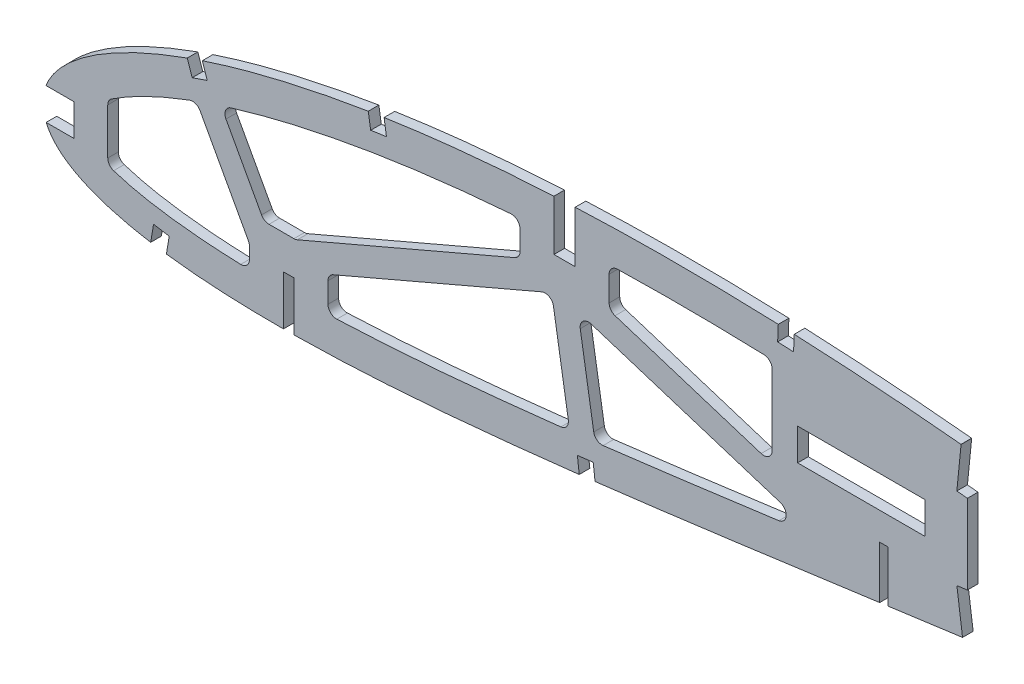
SolidWorks part; units mm, degrees
material "Plywood"
ref_plane "Front Plane" through (0, 0, 0) normal (0, 0, 1) x (1, 0, 0)
ref_plane "Top Plane" through (0, 0, 0) normal (0, 1, 0) x (1, 0, 0)
ref_plane "Right Plane" through (0, 0, 0) normal (1, 0, 0) x (0, 0, -1)
curve "Curve1"
  spline degree 3 poles (452.1031, 0.7048, 0) (452.0685, 0.7262, 0) (451.9301, 0.8117, 0) (451.6183, 1.003, 0) (451.099, 1.3216, 0) (450.372, 1.7653, 0) (449.438, 2.3329, 0) (448.2963, 3.0204, 0) (446.9478, 3.8257, 0) (445.3928, 4.7448, 0) (443.6314, 5.7736, 0) (441.6643, 6.9077, 0) (439.4916, 8.1409, 0) (437.1143, 9.468, 0) (434.5331, 10.8828, 0) (431.7485, 12.3789, 0) (428.7615, 13.9486, 0) (425.5733, 15.5853, 0) (422.1844, 17.2798, 0) (418.5964, 19.0251, 0) (414.8106, 20.8125, 0) (410.8282, 22.6325, 0) (406.6515, 24.4776, 0) (402.2816, 26.3365, 0) (397.7212, 28.201, 0) (392.972, 30.0605, 0) (388.0369, 31.9065, 0) (382.9178, 33.7272, 0) (377.6186, 35.5144, 0) (372.1418, 37.2567, 0) (366.4913, 38.9446, 0) (360.6704, 40.5671, 0) (354.684, 42.1159, 0) (348.5359, 43.5797, 0) (342.2312, 44.9487, 0) (335.775, 46.2147, 0) (329.1727, 47.3651, 0) (322.4425, 48.3989, 0) (315.6929, 49.2588, 0) (308.9571, 50.1023, 0) (302.2314, 50.8946, 0) (295.4235, 51.6533, 0) (288.5399, 52.3742, 0) (281.5875, 53.055, 0) (274.5733, 53.6928, 0) (267.5046, 54.2857, 0) (260.3883, 54.8303, 0) (253.2318, 55.3259, 0) (246.0422, 55.768, 0) (238.8272, 56.1563, 0) (231.5941, 56.4881, 0) (224.3504, 56.7611, 0) (217.1039, 56.9737, 0) (209.862, 57.1238, 0) (202.6326, 57.2105, 0) (195.4232, 57.2315, 0) (188.2416, 57.1863, 0) (181.0954, 57.0734, 0) (173.9924, 56.8912, 0) (166.9401, 56.6395, 0) (159.9462, 56.3182, 0) (153.0184, 55.9248, 0) (146.164, 55.4618, 0) (139.3909, 54.9271, 0) (132.7063, 54.3206, 0) (126.1174, 53.645, 0) (119.6314, 52.8983, 0) (113.2554, 52.0826, 0) (106.9962, 51.1996, 0) (100.8609, 50.2488, 0) (94.8561, 49.2329, 0) (88.9882, 48.153, 0) (83.2635, 47.0122, 0) (77.6882, 45.8109, 0) (72.2682, 44.5525, 0) (67.0092, 43.2395, 0) (61.9167, 41.874, 0) (56.9959, 40.4594, 0) (52.2519, 38.999, 0) (47.6902, 37.4943, 0) (43.3141, 35.951, 0) (39.1291, 34.3702, 0) (35.1384, 32.7568, 0) (31.3466, 31.113, 0) (27.7567, 29.4439, 0) (24.3726, 27.7512, 0) (21.1967, 26.0397, 0) (18.2324, 24.3122, 0) (15.4823, 22.5717, 0) (12.9477, 20.8227, 0) (10.632, 19.0664, 0) (8.5361, 17.307, 0) (6.6613, 15.5474, 0) (5.0102, 13.7886, 0) (3.5829, 12.0339, 0) (2.3811, 10.2847, 0) (1.4051, 8.5424, 0) (0.6571, 6.8085, 0) (0.1363, 5.084, 0) (-0.1488, 3.3712, 0) (-0.2197, 1.669, 0) (-0.0731, 0.5555, 0) (0, 0, 0) knots 0 0 0 0 0.000254 0.001015 0.002283 0.004057 0.006331 0.009105 0.012374 0.016134 0.02038 0.025106 0.030306 0.035972 0.0421 0.048678 0.055702 0.06316 0.071046 0.07935 0.088063 0.097176 0.106678 0.116562 0.126814 0.137428 0.148394 0.1597 0.171338 0.183298 0.19557 0.208144 0.221012 0.234162 0.247587 0.261277 0.275223 0.289414 0.303771 0.317689 0.331784 0.34604 0.360444 0.374983 0.38964 0.404403 0.419257 0.434187 0.449177 0.464215 0.479284 0.49437 0.509458 0.524532 0.539579 0.554583 0.56953 0.584403 0.599191 0.613877 0.628447 0.642889 0.657186 0.671326 0.685294 0.699078 0.712665 0.726043 0.739198 0.752118 0.764792 0.777208 0.789356 0.801224 0.812804 0.824083 0.835055 0.84571 0.856038 0.866034 0.875689 0.884998 0.893953 0.902553 0.910789 0.918661 0.926166 0.933303 0.940071 0.946475 0.952518 0.958205 0.963547 0.968557 0.97325 0.977651 0.981787 0.985694 0.989415 0.993001 0.996508 1 1 1 1
curve "Curve2"
  spline degree 3 poles (0, 0, 0) (0.1161, -0.5481, 0) (0.3488, -1.6467, 0) (0.9811, -3.2283, 0) (1.8173, -4.7487, 0) (2.8749, -6.2038, 0) (4.147, -7.5932, 0) (5.6306, -8.9184, 0) (7.3243, -10.1787, 0) (9.226, -11.3735, 0) (11.3328, -12.5041, 0) (13.6425, -13.5697, 0) (16.1528, -14.5701, 0) (18.8611, -15.5039, 0) (21.764, -16.3724, 0) (24.8588, -17.1737, 0) (28.1419, -17.9088, 0) (31.6103, -18.5759, 0) (35.26, -19.1755, 0) (39.0874, -19.7075, 0) (43.0885, -20.172, 0) (47.2594, -20.5682, 0) (51.596, -20.8969, 0) (56.0938, -21.1583, 0) (60.7487, -21.3533, 0) (65.556, -21.481, 0) (70.5112, -21.5436, 0) (75.6096, -21.5419, 0) (80.8464, -21.4754, 0) (86.2171, -21.3479, 0) (91.7164, -21.1586, 0) (97.3395, -20.9096, 0) (103.0813, -20.6036, 0) (108.9365, -20.2416, 0) (114.9002, -19.8251, 0) (120.967, -19.3576, 0) (127.1315, -18.8401, 0) (133.3883, -18.2757, 0) (139.7319, -17.6673, 0) (146.1567, -17.0167, 0) (152.6572, -16.327, 0) (159.2275, -15.6004, 0) (165.862, -14.8409, 0) (172.5546, -14.0497, 0) (179.2998, -13.2315, 0) (186.0911, -12.3877, 0) (192.923, -11.5217, 0) (199.7891, -10.6375, 0) (206.6832, -9.7349, 0) (213.5994, -8.8205, 0) (220.5311, -7.8935, 0) (227.4721, -6.9586, 0) (234.4161, -6.0188, 0) (241.3564, -5.0743, 0) (248.2868, -4.1291, 0) (255.2009, -3.1857, 0) (262.0918, -2.2442, 0) (268.9535, -1.3094, 0) (275.779, -0.3811, 0) (282.5619, 0.5389, 0) (289.2958, 1.4477, 0) (295.9744, 2.3443, 0) (302.5907, 3.228, 0) (309.138, 4.0992, 0) (315.5119, 4.9314, 0) (321.6955, 5.769, 0) (327.7099, 6.4556, 0) (333.6493, 7.0417, 0) (339.52, 7.5222, 0) (345.315, 7.9041, 0) (351.0275, 8.19, 0) (356.6509, 8.3839, 0) (362.1779, 8.4917, 0) (367.6017, 8.516, 0) (372.9148, 8.4647, 0) (378.1105, 8.3417, 0) (383.1813, 8.1528, 0) (388.1203, 7.9042, 0) (392.9205, 7.6027, 0) (397.5745, 7.2527, 0) (402.076, 6.8625, 0) (406.4179, 6.4377, 0) (410.5937, 5.9833, 0) (414.5972, 5.5086, 0) (418.4221, 5.0169, 0) (422.0625, 4.5163, 0) (425.5126, 4.0117, 0) (428.7669, 3.5097, 0) (431.8204, 3.015, 0) (434.6681, 2.5342, 0) (437.3055, 2.0718, 0) (439.7281, 1.6323, 0) (441.9324, 1.2212, 0) (443.9143, 0.8406, 0) (445.6709, 0.4968, 0) (447.199, 0.1913, 0) (448.4964, -0.0716, 0) (449.5609, -0.2909, 0) (450.3908, -0.463, 0) (450.9844, -0.5881, 0) (451.3411, -0.6626, 0) (451.4997, -0.6964, 0) (451.5393, -0.7048, 0) knots 0 0 0 0 0.003638 0.007293 0.011028 0.014901 0.018963 0.023258 0.027821 0.032679 0.037853 0.043362 0.049215 0.055422 0.061989 0.068918 0.076211 0.083868 0.091887 0.100266 0.109 0.118085 0.127515 0.137285 0.147388 0.157816 0.168563 0.179619 0.190977 0.202627 0.21456 0.226767 0.239236 0.251959 0.264924 0.27812 0.291536 0.30516 0.318981 0.332985 0.347163 0.361499 0.375981 0.390597 0.405333 0.420175 0.43511 0.450124 0.465203 0.480333 0.495501 0.51069 0.525887 0.541078 0.556247 0.571382 0.586466 0.601485 0.616424 0.631269 0.646007 0.660621 0.675098 0.689423 0.703582 0.716908 0.730009 0.742952 0.755726 0.76832 0.780724 0.792927 0.804916 0.816679 0.828204 0.839475 0.850481 0.861208 0.871639 0.881763 0.891564 0.901027 0.910139 0.918884 0.927249 0.935221 0.942785 0.949928 0.956638 0.962904 0.968712 0.974054 0.978918 0.983297 0.98718 0.990561 0.993433 0.995791 0.99763 0.998946 0.999737 1 1 1 1
sketch "Sketch1" plane through (0, 0, 0) normal (0, 0, 1) x (1, 0, 0)
  line L24 (435.3301, 0.6787) -> (439.1729, -1.6142)
  line L25 (434.7872, -0.6787) -> (439.1729, -1.6142)
  spline S4 degree 3 poles (0, 0) (0.1118, -0.5277) (0.3359, -1.5856) (0.9447, -3.1085) (1.7499, -4.5725) (2.7683, -5.9736) (3.9931, -7.3115) (5.4217, -8.5876) (7.0526, -9.8011) (8.8837, -10.9516) (10.9124, -12.0402) (13.1363, -13.0663) (15.5535, -14.0296) (18.1613, -14.9287) (20.9565, -15.765) (23.9365, -16.5366) (27.0978, -17.2444) (30.4375, -17.8867) (33.9519, -18.4641) (37.6373, -18.9763) (41.49, -19.4236) (45.5061, -19.8051) (49.6818, -20.1216) (54.0128, -20.3734) (58.4949, -20.5611) (63.1239, -20.6841) (67.8952, -20.7443) (72.8045, -20.7427) (77.847, -20.6787) (83.0184, -20.5559) (88.3137, -20.3736) (93.7282, -20.1339) (99.2569, -19.8392) (104.895, -19.4906) (110.6374, -19.0896) (116.4791, -18.6394) (122.4149, -18.1411) (128.4396, -17.5977) (134.5478, -17.0118) (140.7343, -16.3853) (146.9936, -15.7212) (153.3201, -15.0216) (159.7085, -14.2903) (166.1528, -13.5285) (172.6478, -12.7406) (179.1872, -11.9281) (185.7655, -11.0942) (192.377, -10.2428) (199.0153, -9.3738) (205.6749, -8.4933) (212.3494, -7.6007) (219.0329, -6.7005) (225.7193, -5.7955) (232.4021, -4.886) (239.0753, -3.9759) (245.7329, -3.0675) (252.3682, -2.161) (258.9753, -1.2608) (265.5476, -0.3669) (272.0789, 0.5189) (278.563, 1.394) (284.9937, 2.2573) (291.3645, 3.1082) (297.669, 3.9471) (303.8064, 4.7484) (309.7606, 5.555) (315.5518, 6.2161) (321.2709, 6.7805) (326.9238, 7.2431) (332.5038, 7.6108) (338.0044, 7.8861) (343.4191, 8.0729) (348.7411, 8.1767) (353.9637, 8.2001) (359.0797, 8.1506) (364.0826, 8.0323) (368.9653, 7.8503) (373.7211, 7.6109) (378.3431, 7.3206) (382.8245, 6.9836) (387.159, 6.6079) (391.3398, 6.1989) (395.3607, 5.7613) (399.2157, 5.3043) (402.8986, 4.8308) (406.404, 4.3487) (409.7261, 3.8629) (412.8597, 3.3795) (415.7999, 2.9031) (418.5419, 2.4402) (421.0815, 1.9949) (423.4142, 1.5717) (425.5368, 1.1759) (427.445, 0.8095) (429.1365, 0.4784) (430.6079, 0.1842) (431.8572, -0.0689) (432.8822, -0.2801) (433.6813, -0.4458) (434.2529, -0.5663) (434.5964, -0.638) (434.749, -0.6706) (434.7872, -0.6787) knots 0 0 0 0 0.003638 0.007293 0.011028 0.014901 0.018963 0.023258 0.027821 0.032679 0.037853 0.043362 0.049215 0.055422 0.061989 0.068918 0.076211 0.083868 0.091887 0.100266 0.109 0.118085 0.127515 0.137285 0.147388 0.157816 0.168563 0.179619 0.190977 0.202627 0.21456 0.226767 0.239236 0.251959 0.264924 0.27812 0.291536 0.30516 0.318981 0.332985 0.347163 0.361499 0.375981 0.390597 0.405333 0.420175 0.43511 0.450124 0.465203 0.480333 0.495501 0.51069 0.525887 0.541078 0.556247 0.571382 0.586466 0.601485 0.616424 0.631269 0.646007 0.660621 0.675098 0.689423 0.703582 0.716908 0.730009 0.742952 0.755726 0.76832 0.780724 0.792927 0.804916 0.816679 0.828204 0.839475 0.850481 0.861208 0.871639 0.881763 0.891564 0.901027 0.910139 0.918884 0.927249 0.935221 0.942785 0.949928 0.956638 0.962904 0.968712 0.974054 0.978918 0.983297 0.98718 0.990561 0.993433 0.995791 0.99763 0.998946 0.999737 1 1 1 1
  spline S5 degree 3 poles (435.3301, 0.6787) (435.2968, 0.6993) (435.1635, 0.7816) (434.8632, 0.9658) (434.3632, 1.2726) (433.6632, 1.6998) (432.7638, 2.2463) (431.6645, 2.9084) (430.3661, 3.6837) (428.8687, 4.5688) (427.1727, 5.5594) (425.2785, 6.6514) (423.1865, 7.8389) (420.8974, 9.1168) (418.4119, 10.4791) (415.7306, 11.9197) (412.8545, 13.4311) (409.7845, 15.0071) (406.5213, 16.6387) (403.0665, 18.3192) (399.4211, 20.0403) (395.5865, 21.7928) (391.5647, 23.5695) (387.357, 25.3594) (382.9657, 27.1547) (378.3927, 28.9452) (373.6407, 30.7228) (368.7116, 32.4759) (363.609, 34.1968) (358.3353, 35.8745) (352.8945, 37.4998) (347.2896, 39.0621) (341.5252, 40.5534) (335.6052, 41.9629) (329.5344, 43.2811) (323.3177, 44.5002) (316.9603, 45.6079) (310.4799, 46.6033) (303.9807, 47.4313) (297.4948, 48.2435) (291.0186, 49.0064) (284.4633, 49.737) (277.8351, 50.4311) (271.1406, 51.0867) (264.3866, 51.7008) (257.5802, 52.2717) (250.7279, 52.7961) (243.8369, 53.2733) (236.914, 53.699) (229.9667, 54.0729) (223.0019, 54.3924) (216.027, 54.6553) (209.0493, 54.86) (202.0761, 55.0045) (195.1149, 55.088) (188.173, 55.1082) (181.2578, 55.0647) (174.3767, 54.956) (167.5373, 54.7806) (160.7467, 54.5381) (154.0122, 54.2288) (147.3414, 53.85) (140.7414, 53.4041) (134.2195, 52.8893) (127.7829, 52.3053) (121.4385, 51.6548) (115.1931, 50.9357) (109.0536, 50.1503) (103.0266, 49.3001) (97.119, 48.3846) (91.3369, 47.4064) (85.6868, 46.3665) (80.1745, 45.2681) (74.806, 44.1113) (69.5871, 42.8996) (64.5231, 41.6353) (59.6196, 40.3205) (54.8814, 38.9584) (50.3134, 37.5521) (45.9209, 36.1032) (41.7071, 34.6172) (37.6774, 33.0951) (33.8348, 31.5415) (30.1837, 29.9587) (26.7269, 28.3515) (23.4684, 26.7216) (20.4104, 25.0737) (17.5559, 23.4102) (14.9079, 21.7343) (12.4673, 20.0502) (10.2376, 18.359) (8.2194, 16.6649) (6.4142, 14.9706) (4.8244, 13.2771) (3.45, 11.5875) (2.2928, 9.9031) (1.353, 8.2255) (0.6327, 6.5559) (0.1312, 4.8953) (-0.1433, 3.2462) (-0.2116, 1.607) (-0.0704, 0.5349) (0, 0) knots 0 0 0 0 0.000254 0.001015 0.002283 0.004057 0.006331 0.009105 0.012374 0.016134 0.02038 0.025106 0.030306 0.035972 0.0421 0.048678 0.055702 0.06316 0.071046 0.07935 0.088063 0.097176 0.106678 0.116562 0.126814 0.137428 0.148394 0.1597 0.171338 0.183298 0.19557 0.208144 0.221012 0.234162 0.247587 0.261277 0.275223 0.289414 0.303771 0.317689 0.331784 0.34604 0.360444 0.374983 0.38964 0.404403 0.419257 0.434187 0.449177 0.464215 0.479284 0.49437 0.509458 0.524532 0.539579 0.554583 0.56953 0.584403 0.599191 0.613877 0.628447 0.642889 0.657186 0.671326 0.685294 0.699078 0.712665 0.726043 0.739198 0.752118 0.764792 0.777208 0.789356 0.801224 0.812804 0.824083 0.835055 0.84571 0.856038 0.866034 0.875689 0.884998 0.893953 0.902553 0.910789 0.918661 0.926166 0.933303 0.940071 0.946475 0.952518 0.958205 0.963547 0.968557 0.97325 0.977651 0.981787 0.985694 0.989415 0.993001 0.996508 1 1 1 1
extrude "Boss-Extrude1" add sketch "Sketch1" along normal blind 3.175
sketch "Sketch2" plane through (0, 0, 0) normal (0, 0, -1) x (-1, 0, 0)
  line L0 (-252.7944, 13.2215) -> (-250.2544, 13.2215)
  line L1 (-250.2544, -2.1152) -> (-250.2544, -3.9863)
  line L2 (-252.7944, 13.2215) -> (-252.7944, -2.1152)
  line L4 (-250.2544, -3.9863) -> (-252.7944, -3.0508)
  line L5 (-252.7944, -3.0508) -> (-252.7944, -2.1152)
  line L7 (-159.1319, 54.4222) -> (-159.1319, 39.0391)
  line L8 (-159.1319, 39.0391) -> (-152.7819, 39.0391)
  line L9 (-152.7819, 54.4222) -> (-152.7819, 57.6454)
  line L10 (-74.9944, -5.9288) -> (-74.9944, -20.1418)
  line L12 (-152.7819, 57.6454) -> (-159.1319, 55.5409)
  line L13 (-159.1319, 55.5409) -> (-159.1319, 54.4222)
  line L14 (-71.8194, -5.9288) -> (-71.8194, -20.1418)
  line L16 (-74.9944, -5.9288) -> (-71.8194, -5.9288)
  line L17 (-71.8194, -20.1418) -> (-71.8194, -22.1459)
  line L19 (-152.7819, 54.4222) -> (-152.7819, 39.0391)
  line L20 (-71.8194, -22.1459) -> (-74.9944, -20.9764)
  line L21 (-74.9944, -20.9764) -> (-74.9944, -20.1418)
  line L22 (-250.2544, 13.2215) -> (-250.2544, -2.1152)
extrude "Cut-Extrude1" cut sketch "Sketch2" against normal blind 7.62
sketch "Sketch3" plane through (0, 0, 0) normal (0, 0, -1) x (-1, 0, 0)
  circle A1 centre (-292.3838, 26.2554) radius 6.35
extrude "Cut-Extrude2" cut sketch "Sketch3" against normal blind 7.62
sketch "Sketch4" plane through (0, 0, 3.175) normal (0, 0, 1) x (1, 0, 0)
  line L0 (274.6066, 50.6647) -> (273.3497, 38.0281)
  line L1 (274.6066, 50.6647) -> (273.3497, 38.0281)
  line L2 (276.5088, 37.7139) -> (277.7874, 50.3428)
  line L3 (276.5088, 37.7139) -> (277.7874, 50.3428)
  line L4 (278.2022, 1.3477) -> (276.5088, 13.9346)
  line L5 (278.2022, 1.3477) -> (276.5088, 13.9346)
  line L6 (273.3622, 13.5108) -> (275.0576, 0.9245)
  line L7 (273.3622, 13.5108) -> (275.0576, 0.9245)
  line L8 (224.4836, 49.6431) -> (224.6991, 54.396)
  line L9 (224.4836, 49.6431) -> (224.6991, 54.396)
  line L10 (165.0827, -13.6872) -> (164.5226, -8.9534)
  line L11 (165.0827, -13.6872) -> (164.5226, -8.9534)
  line L12 (102.6454, 44.5104) -> (101.9324, 49.2278)
  line L13 (102.6454, 44.5104) -> (101.9324, 49.2278)
  line L14 (36.8388, -18.5812) -> (37.6418, -13.8082)
  line L15 (36.8388, -18.5812) -> (37.6418, -13.8082)
  line L16 (49.0205, 32.2539) -> (47.492, 36.7462)
  line L17 (49.0205, 32.2539) -> (47.492, 36.7462)
  line L18 (9.0835, -2.7147) -> (9.0835, 6.8103)
  line L19 (9.0835, -2.7147) -> (9.0835, 6.8103)
  line L20 (-0.4415, 6.8103) -> (9.0835, 6.8103)
  line L21 (-0.4415, 6.8103) -> (9.0835, 6.8103)
  line L22 (32.9524, -13.0236) -> (32.1659, -17.7312)
  line L23 (32.9524, -13.0236) -> (32.1659, -17.7312)
  line L24 (97.1897, 48.4826) -> (97.9364, 43.7986)
  line L25 (97.1897, 48.4826) -> (97.9364, 43.7986)
  line L26 (159.7931, -9.5131) -> (160.3442, -14.2455)
  line L27 (159.7931, -9.5131) -> (160.3442, -14.2455)
  line L28 (42.9896, 35.1929) -> (44.512, 30.7197)
  line L29 (42.9896, 35.1929) -> (44.512, 30.7197)
  line L30 (-0.4415, -2.7147) -> (9.0835, -2.7147)
  line L31 (-0.4415, -2.7147) -> (9.0835, -2.7147)
  line L32 (219.9134, 54.5992) -> (219.7258, 49.8498)
  line L33 (219.9134, 54.5992) -> (219.7258, 49.8498)
  line L34 (276.5088, 13.9346) -> (276.5088, 37.7139)
  line L35 (273.3497, 38.0281) -> (276.5088, 37.7139)
  line L36 (276.5088, 13.9346) -> (273.3622, 13.5108)
  line L37 (275.0576, 0.9245) -> (278.2022, 1.3477)
  line L38 (219.7258, 49.8498) -> (224.4836, 49.6431)
  line L39 (224.6991, 54.396) -> (219.9134, 54.5992)
  line L40 (159.7931, -9.5131) -> (164.5226, -8.9534)
  line L41 (165.0827, -13.6872) -> (160.3442, -14.2455)
  line L42 (42.9896, 35.1929) -> (47.492, 36.7462)
  line L43 (44.512, 30.7197) -> (49.0205, 32.2539)
  line L44 (97.1897, 48.4826) -> (101.9324, 49.2278)
  line L45 (102.6454, 44.5104) -> (97.9364, 43.7986)
  line L46 (-0.4415, 6.8103) -> (-0.4415, -2.7147)
  line L47 (32.9524, -13.0236) -> (37.6418, -13.8082)
  line L48 (36.8388, -18.5812) -> (32.1659, -17.7312)
  line L49 (277.7874, 50.3428) -> (274.6066, 50.6647)
  line L50 (275.0576, 0.9245) -> (275.0576, -18.8331)
  line L51 (225.7088, 31.0179) -> (263.8088, 31.0179)
  line L52 (225.7088, 31.0179) -> (225.7088, 21.4929)
  line L53 (225.7088, 21.4929) -> (263.8088, 21.4929)
  line L54 (263.8088, 31.0179) -> (263.8088, 21.4929)
  line L55 (446.0862, 59.9441) -> (446.0862, -18.8331)
  line L56 (446.0862, -18.8331) -> (275.0576, -18.8331)
  line L57 (274.6066, 50.6647) -> (274.6066, 59.9441)
  line L58 (274.6066, 59.9441) -> (446.0862, 59.9441)
  line L59 (32.1659, -17.7312) -> (31.5691, -21.3035)
  line L60 (31.5691, -21.3035) -> (36.2028, -22.0776)
  line L61 (36.2028, -22.0776) -> (36.8388, -18.5812)
  circle A0 centre (292.3838, 26.2554) radius 6.35 construction
  circle A1 centre (292.3838, 26.2554) radius 6.35
  point P40 (263.8088, 26.2554)
  dimension "D1" = 9.525
  dimension "D2" = 38.1
  dimension "D3" = 12.7
extrude "Cut-Extrude3" cut sketch "Sketch4" against normal through all
sketch "Sketch5" plane through (0, 0, 3.175) normal (0, 0, 1) x (1, 0, 0)
  line L0 (0.7643, 6.8103) -> (9.0835, 6.8103) construction
  line L1 (0.7643, 6.8103) -> (9.0835, 6.8103) construction
  line L2 (0.803, -2.7147) -> (9.0835, -2.7147) construction
  line L3 (0.803, -2.7147) -> (9.0835, -2.7147) construction
  line L4 (273.3622, 13.5108) -> (275.0576, 0.9245) construction
  line L5 (273.3622, 13.5108) -> (275.0576, 0.9245) construction
  line L6 (274.6066, 50.6647) -> (273.3497, 38.0281) construction
  line L7 (274.6066, 50.6647) -> (273.3497, 38.0281) construction
  line L8 (19.2435, 12.3749) -> (19.2435, -4.5391)
  line L9 (9.0835, -2.7147) -> (9.0835, 6.8103) construction
  line L10 (61.6594, 4.2312) -> (46.7663, 31.4868) construction
  line L11 (44.512, 30.7197) -> (49.0205, 32.2539) construction
  line L12 (85.1544, 4.2312) -> (142.6219, 28.8791) construction
  line L13 (169.2919, 28.8791) -> (240.0944, 6.4173) construction
  line L14 (155.9569, 28.8791) -> (162.1578, -9.2332) construction
  line L15 (159.7931, -9.5131) -> (164.5226, -8.9534) construction
  line L16 (66.0011, 4.2312) -> (50.1097, 33.3137)
  line L17 (85.1544, 0.0856) -> (152.2877, 28.8791)
  line L18 (152.1093, 28.8026) -> (158.3973, -9.8451)
  line L19 (159.9871, 27.8339) -> (238.9423, 2.7857)
  line L20 (61.6594, -3.7144) -> (43.4229, 29.6599)
  line L21 (75.4887, 4.2312) -> (142.6219, 33.0248)
  line L22 (159.7175, 29.4909) -> (165.9184, -8.6214)
  line L23 (169.2919, 32.8762) -> (241.2466, 10.049)
  line L24 (65.0029, 6.0582) -> (50.1097, 33.3137) construction
  line L25 (58.316, 2.4043) -> (43.4229, 29.6599) construction
  line L26 (83.6526, 7.7327) -> (141.1201, 32.3806) construction
  line L27 (86.6562, 0.7297) -> (144.1237, 25.3776) construction
  line L28 (152.1964, 28.2673) -> (158.3973, -9.8451) construction
  line L29 (168.1398, 25.2475) -> (238.9423, 2.7857) construction
  line L30 (170.4441, 32.5107) -> (241.2466, 10.049) construction
  line L35 (85.1544, 4.2312) -> (85.1544, -20.7123)
  line L36 (61.6594, 4.2312) -> (85.1544, 4.2312)
  line L37 (61.6594, -20.7377) -> (61.6594, 4.2312)
  line L38 (85.1544, 4.2312) -> (85.1544, -20.7123)
  line L39 (61.6594, 4.2312) -> (85.1544, 4.2312)
  line L40 (61.6594, -10.4783) -> (61.6594, 4.2312)
  line L46 (240.0944, -2.4499) -> (240.0944, 13.2215)
  line L47 (169.2919, 54.4587) -> (169.2919, 28.8791)
  line L48 (169.2919, 28.8791) -> (142.6219, 28.8791)
  line L49 (142.6219, 28.8791) -> (142.6219, 54.1523)
  line L50 (169.2919, 44.6566) -> (169.2919, 28.8791)
  line L51 (169.2919, 28.8791) -> (142.6219, 28.8791)
  line L52 (142.6219, 28.8791) -> (142.6219, 43.3411)
  line L53 (240.0944, 6.4173) -> (240.0944, 13.8729)
  line L62 (263.8088, 38.6379) -> (218.0888, 38.6379)
  line L63 (218.0888, 38.6379) -> (218.0888, 13.8729)
  line L64 (218.0888, 13.8729) -> (263.8088, 13.8729)
  line L66 (218.0888, 44.4072) -> (218.0888, 13.8729)
  line L67 (218.0888, 13.8729) -> (240.0944, 13.8729)
  spline S4 degree 3 poles (1523.9168, 1677.8723) (459.4041, -20.0575) (448.5517, -7.4305) (434.8632, 0.9658) (434.3632, 1.2726) (433.6632, 1.6998) (432.7638, 2.2463) (431.6645, 2.9084) (430.3661, 3.6837) (428.8687, 4.5688) (427.1727, 5.5594) (425.2785, 6.6514) (423.1865, 7.8389) (420.8974, 9.1168) (418.4119, 10.4791) (415.7306, 11.9197) (412.8545, 13.4311) (409.7845, 15.0071) (406.5213, 16.6387) (403.0665, 18.3192) (399.4211, 20.0403) (395.5865, 21.7928) (391.5647, 23.5695) (387.357, 25.3594) (382.9657, 27.1547) (378.3927, 28.9452) (373.6407, 30.7228) (368.7116, 32.4759) (363.609, 34.1968) (358.3353, 35.8745) (352.8945, 37.4998) (347.2896, 39.0621) (341.5252, 40.5534) (335.6052, 41.9629) (329.5344, 43.2811) (323.3177, 44.5002) (316.9603, 45.6079) (310.4799, 46.6033) (303.9807, 47.4313) (297.4948, 48.2435) (291.0186, 49.0064) (284.4633, 49.737) (277.8351, 50.4311) (271.1406, 51.0867) (264.3866, 51.7008) (257.5802, 52.2717) (250.7279, 52.7961) (243.8369, 53.2733) (236.914, 53.699) (229.9667, 54.0729) (223.0019, 54.3924) (216.027, 54.6553) (209.0493, 54.86) (202.0761, 55.0045) (195.1149, 55.088) (188.173, 55.1082) (181.2578, 55.0647) (174.3767, 54.956) (167.5373, 54.7806) (160.7467, 54.5381) (154.0122, 54.2288) (147.3414, 53.85) (140.7414, 53.4041) (134.2195, 52.8893) (127.7829, 52.3053) (121.4385, 51.6548) (115.1931, 50.9357) (109.0536, 50.1503) (103.0266, 49.3001) (97.119, 48.3846) (91.3369, 47.4064) (85.6868, 46.3665) (80.1745, 45.2681) (74.806, 44.1113) (69.5871, 42.8996) (64.5231, 41.6353) (59.6196, 40.3205) (54.8814, 38.9584) (50.3134, 37.5521) (45.9209, 36.1032) (41.7071, 34.6172) (37.6774, 33.0951) (33.8348, 31.5415) (30.1837, 29.9587) (26.7269, 28.3515) (23.4684, 26.7216) (20.4104, 25.0737) (17.5559, 23.4102) (14.9079, 21.7343) (12.4673, 20.0502) (10.2376, 18.359) (8.2194, 16.6649) (6.4142, 14.9706) (4.8244, 13.2771) (3.45, 11.5875) (2.2928, 9.9031) (1.353, 8.2255) (0.6327, 6.5559) (0.1312, 4.8953) (-0.1433, 3.2462) (-1.0017, -17.3492) (61.8716, -33.4146) (-1991.1542, -180.949) knots -0.101807 -0.101807 -0.101807 -0.101807 0.000254 0.001015 0.002283 0.004057 0.006331 0.009105 0.012374 0.016134 0.02038 0.025106 0.030306 0.035972 0.0421 0.048678 0.055702 0.06316 0.071046 0.07935 0.088063 0.097176 0.106678 0.116562 0.126814 0.137428 0.148394 0.1597 0.171338 0.183298 0.19557 0.208144 0.221012 0.234162 0.247587 0.261277 0.275223 0.289414 0.303771 0.317689 0.331784 0.34604 0.360444 0.374983 0.38964 0.404403 0.419257 0.434187 0.449177 0.464215 0.479284 0.49437 0.509458 0.524532 0.539579 0.554583 0.56953 0.584403 0.599191 0.613877 0.628447 0.642889 0.657186 0.671326 0.685294 0.699078 0.712665 0.726043 0.739198 0.752118 0.764792 0.777208 0.789356 0.801224 0.812804 0.824083 0.835055 0.84571 0.856038 0.866034 0.875689 0.884998 0.893953 0.902553 0.910789 0.918661 0.926166 0.933303 0.940071 0.946475 0.952518 0.958205 0.963547 0.968557 0.97325 0.977651 0.981787 0.985694 0.989415 0.993001 0.996508 1.122415 1.122415 1.122415 1.122415 only from (435.3301, 0.6787) to (0, 0) construction
  spline S7 degree 3 poles (-1938.1568, -491.7767) (47.0927, 52.1326) (-6.7204, 16.0645) (0.9447, -3.1085) (1.7499, -4.5725) (2.7683, -5.9736) (3.9931, -7.3115) (5.4217, -8.5876) (7.0526, -9.8011) (8.8837, -10.9516) (10.9124, -12.0402) (13.1363, -13.0663) (15.5535, -14.0296) (18.1613, -14.9287) (20.9565, -15.765) (23.9365, -16.5366) (27.0978, -17.2444) (30.4375, -17.8867) (33.9519, -18.4641) (37.6373, -18.9763) (41.49, -19.4236) (45.5061, -19.8051) (49.6818, -20.1216) (54.0128, -20.3734) (58.4949, -20.5611) (63.1239, -20.6841) (67.8952, -20.7443) (72.8045, -20.7427) (77.847, -20.6787) (83.0184, -20.5559) (88.3137, -20.3736) (93.7282, -20.1339) (99.2569, -19.8392) (104.895, -19.4906) (110.6374, -19.0896) (116.4791, -18.6394) (122.4149, -18.1411) (128.4396, -17.5977) (134.5478, -17.0118) (140.7343, -16.3853) (146.9936, -15.7212) (153.3201, -15.0216) (159.7085, -14.2903) (166.1528, -13.5285) (172.6478, -12.7406) (179.1872, -11.9281) (185.7655, -11.0942) (192.377, -10.2428) (199.0153, -9.3738) (205.6749, -8.4933) (212.3494, -7.6007) (219.0329, -6.7005) (225.7193, -5.7955) (232.4021, -4.886) (239.0753, -3.9759) (245.7329, -3.0675) (252.3682, -2.161) (258.9753, -1.2608) (265.5476, -0.3669) (272.0789, 0.5189) (278.563, 1.394) (284.9937, 2.2573) (291.3645, 3.1082) (297.669, 3.9471) (303.8064, 4.7484) (309.7606, 5.555) (315.5518, 6.2161) (321.2709, 6.7805) (326.9238, 7.2431) (332.5038, 7.6108) (338.0044, 7.8861) (343.4191, 8.0729) (348.7411, 8.1767) (353.9637, 8.2001) (359.0797, 8.1506) (364.0826, 8.0323) (368.9653, 7.8503) (373.7211, 7.6109) (378.3431, 7.3206) (382.8245, 6.9836) (387.159, 6.6079) (391.3398, 6.1989) (395.3607, 5.7613) (399.2157, 5.3043) (402.8986, 4.8308) (406.404, 4.3487) (409.7261, 3.8629) (412.8597, 3.3795) (415.7999, 2.9031) (418.5419, 2.4402) (421.0815, 1.9949) (423.4142, 1.5717) (425.5368, 1.1759) (427.445, 0.8095) (429.1365, 0.4784) (430.6079, 0.1842) (431.8572, -0.0689) (432.8822, -0.2801) (433.6813, -0.4458) (434.2529, -0.5663) (448.3411, -3.5068) (461.0644, -11.9601) (889.5705, 1946.1435) knots -0.127812 -0.127812 -0.127812 -0.127812 0.003638 0.007293 0.011028 0.014901 0.018963 0.023258 0.027821 0.032679 0.037853 0.043362 0.049215 0.055422 0.061989 0.068918 0.076211 0.083868 0.091887 0.100266 0.109 0.118085 0.127515 0.137285 0.147388 0.157816 0.168563 0.179619 0.190977 0.202627 0.21456 0.226767 0.239236 0.251959 0.264924 0.27812 0.291536 0.30516 0.318981 0.332985 0.347163 0.361499 0.375981 0.390597 0.405333 0.420175 0.43511 0.450124 0.465203 0.480333 0.495501 0.51069 0.525887 0.541078 0.556247 0.571382 0.586466 0.601485 0.616424 0.631269 0.646007 0.660621 0.675098 0.689423 0.703582 0.716908 0.730009 0.742952 0.755726 0.76832 0.780724 0.792927 0.804916 0.816679 0.828204 0.839475 0.850481 0.861208 0.871639 0.881763 0.891564 0.901027 0.910139 0.918884 0.927249 0.935221 0.942785 0.949928 0.956638 0.962904 0.968712 0.974054 0.978918 0.983297 0.98718 0.990561 0.993433 0.995791 0.99763 0.998946 0.999737 1.094845 1.094845 1.094845 1.094845 only from (0, 0) to (434.7872, -0.6787) construction
  spline S8 degree 3 poles (0.803, -2.7147) (0.8566, -2.8383) (1.1411, -3.4655) (1.7499, -4.5725) (2.7683, -5.9736) (3.9931, -7.3115) (5.4217, -8.5876) (7.0526, -9.8011) (8.8837, -10.9516) (10.9124, -12.0402) (13.1363, -13.0663) (15.5535, -14.0296) (18.1613, -14.9287) (20.9565, -15.765) (23.9365, -16.5366) (27.0978, -17.2444) (30.4375, -17.8867) (33.9519, -18.4641) (37.6373, -18.9763) (41.49, -19.4236) (45.5061, -19.8051) (49.6818, -20.1216) (54.0128, -20.3734) (58.4949, -20.5611) (63.1239, -20.6841) (67.8952, -20.7443) (72.8045, -20.7427) (77.847, -20.6787) (83.0184, -20.5559) (88.3137, -20.3736) (93.7282, -20.1339) (99.2569, -19.8392) (104.895, -19.4906) (110.6374, -19.0896) (116.4791, -18.6394) (122.4149, -18.1411) (128.4396, -17.5977) (134.5478, -17.0118) (140.7343, -16.3853) (146.9936, -15.7212) (153.3201, -15.0216) (159.7085, -14.2903) (166.1528, -13.5285) (172.6478, -12.7406) (179.1872, -11.9281) (185.7655, -11.0942) (192.377, -10.2428) (199.0153, -9.3738) (205.6749, -8.4933) (212.3494, -7.6007) (219.0329, -6.7005) (225.7193, -5.7955) (232.4021, -4.886) (239.0753, -3.9759) (245.7329, -3.0675) (252.3682, -2.161) (258.9753, -1.2608) (265.5476, -0.3669) (270.9047, 0.3596) (274.0703, 0.7875) (275.0581, 0.9208) knots 0.006385 0.006385 0.006385 0.006385 0.007293 0.011028 0.014901 0.018963 0.023258 0.027821 0.032679 0.037853 0.043362 0.049215 0.055422 0.061989 0.068918 0.076211 0.083868 0.091887 0.100266 0.109 0.118085 0.127515 0.137285 0.147388 0.157816 0.168563 0.179619 0.190977 0.202627 0.21456 0.226767 0.239236 0.251959 0.264924 0.27812 0.291536 0.30516 0.318981 0.332985 0.347163 0.361499 0.375981 0.390597 0.405333 0.420175 0.43511 0.450124 0.465203 0.480333 0.495501 0.51069 0.525887 0.541078 0.556247 0.571382 0.586466 0.601485 0.616424 0.631269 0.638002 0.638002 0.638002 0.638002 construction
  spline S9 degree 3 poles (274.6145, 50.7446) (273.4626, 50.8575) (270.0595, 51.185) (264.3866, 51.7008) (257.5802, 52.2717) (250.7279, 52.7961) (243.8369, 53.2733) (236.914, 53.699) (229.9667, 54.0729) (223.0019, 54.3924) (216.027, 54.6553) (209.0493, 54.86) (202.0761, 55.0045) (195.1149, 55.088) (188.173, 55.1082) (181.2578, 55.0647) (174.3767, 54.956) (167.5373, 54.7806) (160.7467, 54.5381) (154.0122, 54.2288) (147.3414, 53.85) (140.7414, 53.4041) (134.2195, 52.8893) (127.7829, 52.3053) (121.4385, 51.6548) (115.1931, 50.9357) (109.0536, 50.1503) (103.0266, 49.3001) (97.119, 48.3846) (91.3369, 47.4064) (85.6868, 46.3665) (80.1745, 45.2681) (74.806, 44.1113) (69.5871, 42.8996) (64.5231, 41.6353) (59.6196, 40.3205) (54.8814, 38.9584) (50.3134, 37.5521) (45.9209, 36.1032) (41.7071, 34.6172) (37.6774, 33.0951) (33.8348, 31.5415) (30.1837, 29.9587) (26.7269, 28.3515) (23.4684, 26.7216) (20.4104, 25.0737) (17.5559, 23.4102) (14.9079, 21.7343) (12.4673, 20.0502) (10.2376, 18.359) (8.2194, 16.6649) (6.4142, 14.9706) (4.8244, 13.2771) (3.45, 11.5875) (2.2928, 9.9031) (1.404, 8.3167) (0.9441, 7.2755) (0.7643, 6.8103) knots 0.36748 0.36748 0.36748 0.36748 0.374983 0.38964 0.404403 0.419257 0.434187 0.449177 0.464215 0.479284 0.49437 0.509458 0.524532 0.539579 0.554583 0.56953 0.584403 0.599191 0.613877 0.628447 0.642889 0.657186 0.671326 0.685294 0.699078 0.712665 0.726043 0.739198 0.752118 0.764792 0.777208 0.789356 0.801224 0.812804 0.824083 0.835055 0.84571 0.856038 0.866034 0.875689 0.884998 0.893953 0.902553 0.910789 0.918661 0.926166 0.933303 0.940071 0.946475 0.952518 0.958205 0.963547 0.968557 0.97325 0.977651 0.981787 0.985018 0.985018 0.985018 0.985018 construction
  spline S10 degree 1 poles (273.6234, 40.633) (10.241, 3.1473) knots 0 0 1 1 construction
  spline S11 degree 3 poles (273.6234, 40.633) (261.8996, 41.7822) (246.3218, 43.0254) (224.858, 44.1754) (212.2098, 44.6377) (195.2259, 44.9816) (179.6649, 44.9617) (164.4565, 44.5306) (154.8005, 44.0998) (146.6761, 43.6349) (139.351, 43.1141) (128.8047, 42.2286) (115.3869, 40.8171) (98.0892, 38.3586) (80.9736, 35.1878) (66.9367, 31.8567) (55.9177, 28.696) (47.7947, 26.0481) (39.8579, 23.0898) (32.1818, 19.7752) (26.1041, 16.671) (22.151, 14.3095) (20.0018, 12.906) (18.72, 12.0134) (17.1919, 10.8896) (15.2717, 9.3616) (13.3943, 7.5998) (12.0434, 6.07) (11.2157, 4.9715) (10.7011, 4.133) (10.4008, 3.5344) (10.2931, 3.2822) (10.241, 3.1473) knots 0.36748 0.36748 0.36748 0.36748 0.444672 0.469815 0.508411 0.527709 0.581332 0.61065 0.627813 0.644976 0.664275 0.676249 0.714845 0.753441 0.792037 0.830634 0.849932 0.86923 0.888528 0.907826 0.927124 0.936773 0.941413 0.946237 0.94865 0.956071 0.96572 0.970545 0.975369 0.980194 0.982606 0.985018 0.985018 0.985018 0.985018 only from (218.0888, 44.4072) to (19.2435, 12.3749)
  spline S12 degree 1 poles (10.1243, 1.3276) (273.699, 10.9895) knots 0 0 1 1 construction
  spline S13 degree 3 poles (10.1243, 1.3276) (10.1575, 1.251) (10.2303, 1.103) (10.4049, 0.8036) (10.7495, 0.3423) (11.4413, -0.3586) (12.685, -1.3632) (14.6996, -2.6013) (16.8832, -3.6135) (18.675, -4.3336) (19.9239, -4.7918) (22.0966, -5.515) (26.2032, -6.6904) (32.7132, -8.0456) (40.8413, -9.1836) (49.0966, -9.9348) (55.3601, -10.273) (60.2441, -10.4459) (63.1254, -10.5167) (70.9778, -10.6322) (83.1615, -10.477) (100.3763, -9.6617) (117.6379, -8.4001) (140.6921, -6.2673) (169.5492, -2.9697) (201.8108, 1.214) (228.1306, 4.7834) (251.2879, 7.9457) (265.2968, 9.8553) (273.699, 10.9895) knots 0.006385 0.006385 0.006385 0.006385 0.008852 0.011319 0.016254 0.021188 0.026123 0.035992 0.044829 0.047296 0.052231 0.05573 0.065599 0.085337 0.105075 0.124813 0.144188 0.149123 0.158992 0.164289 0.203765 0.243241 0.282717 0.322194 0.401146 0.480098 0.542591 0.580755 0.638002 0.638002 0.638002 0.638002 only from (19.2435, -4.5391) to (240.0944, 6.4173)
  dimension "D3" = 10.16
  dimension "D1" = 10.16
  dimension "D2" = 10.16
  dimension "D4" = 10.16
  dimension "D5" = 10.16
  dimension "D6" = 10.16
  dimension "D7" = 7.62
  dimension "D8" = 3.81
  dimension "D9" = 3.81
extrude "Cut-Extrude4" cut sketch "Sketch5" against normal through all contours L8 S13 L40 L20 S11 | L52 S11 L16 L39 L21 | L38 S13 L18 L17 | L22 S13 L19 | L66 S11 L50 L23
fillet "Fillet1" radius 2.54 21 edges at (169.2919, 32.8762, 1.5875) (169.2919, 44.6566, 1.5875) (218.0888, 44.4072, 1.5875) (218.0888, 17.3957, 1.5875) (19.2435, 12.3749, 1.5875) (45.8148, 25.2824, 1.5875) (61.6594, -3.7144, 1.5875) (19.2435, -4.5391, 1.5875) (85.1544, 0.0856, 1.5875) (152.1093, 28.8026, 1.5875) (157.4976, -4.3152, 1.5875) (85.1544, -10.314, 1.5875) (142.6219, 33.0248, 1.5875) (75.4887, 4.2312, 1.5875) (66.0011, 4.2312, 1.5875) (53.1378, 27.7721, 1.5875) (142.6219, 43.3411, 1.5875) (159.9871, 27.8339, 1.5875) (231.282, 5.2159, 1.5875) (165.0725, -3.4222, 1.5875) (61.6594, -10.4783, 1.5875)
move or copy body "Body-Move/Copy1" [suppressed] bodies to move or copy 118 119 parameters "D1"=0, "D2"=0, "D3"=0
